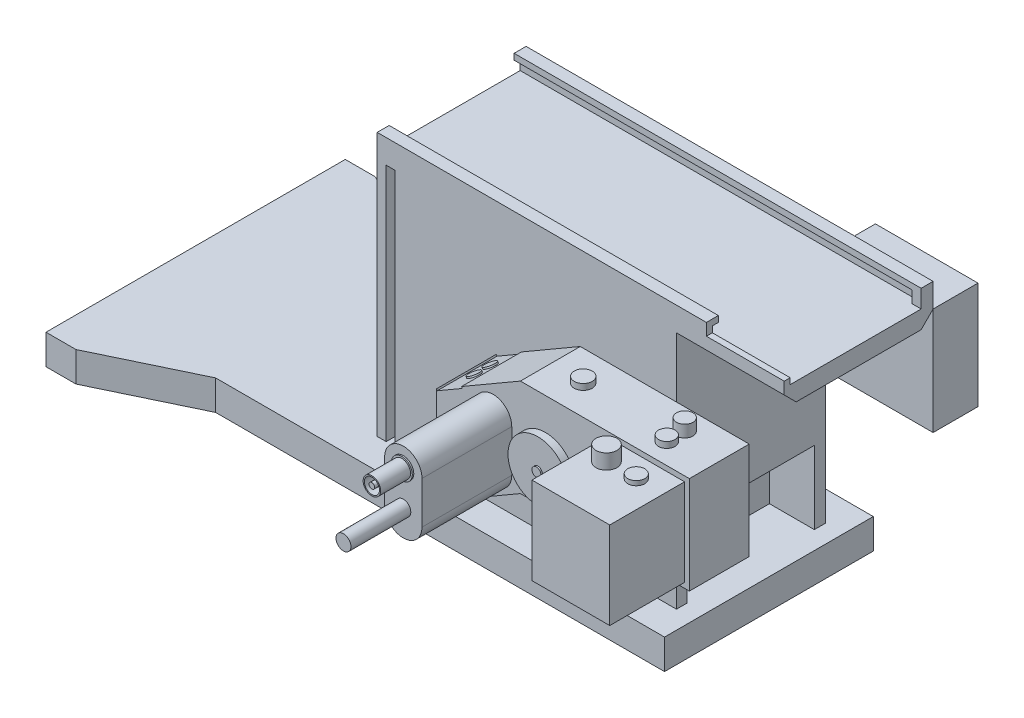
SolidWorks part; units mm, degrees
ref_plane "Front Plane" through (0, 0, 0) normal (0, 0, 1) x (1, 0, 0)
ref_plane "Top Plane" through (0, 0, 0) normal (0, 1, 0) x (1, 0, 0)
ref_plane "Right Plane" through (0, 0, 0) normal (1, 0, 0) x (0, 0, -1)
sketch "Sketch1" plane through (0, 0, 0) normal (0, 1, 0) x (1, 0, 0)
  line L0 (0, 0) -> (0, 100)
  line L1 (0, 100) -> (10, 100)
  line L2 (10, 100) -> (41.5665, 84.882)
  line L3 (41.5665, 84.882) -> (191.5665, 84.882)
  line L5 (191.5665, 15.118) -> (191.5665, 84.882)
  line L6 (41.5665, 15.118) -> (191.5665, 15.118)
  line L7 (10, 0) -> (41.5665, 15.118)
  line L8 (0, 0) -> (10, 0)
extrude "Boss-Extrude1" add sketch "Sketch1" along normal blind 10
sketch "Sketch3" plane through (0, 10, 0) normal (0, 1, 0) x (1, 0, 0)
  line L0 (85.5015, 74.9359) -> (88.5015, 74.9359)
  line L1 (85.5015, 25.1719) -> (88.5015, 25.1719)
  line L2 (85.5015, 74.9359) -> (88.5015, 74.9359)
  line L3 (88.5015, 74.9359) -> (88.5015, 71.9384)
  line L4 (185.5015, 74.9359) -> (185.5015, 25.1719)
  line L5 (91.5015, 28.1694) -> (91.5015, 25.1719)
  line L6 (88.5015, 71.9384) -> (91.5015, 71.9384)
  line L7 (85.5015, 25.1719) -> (85.5015, 74.9359)
  line L8 (91.5015, 71.9384) -> (91.5015, 74.9359)
  line L9 (88.5015, 25.1719) -> (88.5015, 28.1694)
  line L10 (88.5015, 28.1694) -> (91.5015, 28.1694)
  line L11 (91.5015, 74.9359) -> (185.5015, 74.9359)
  line L12 (91.5015, 25.1719) -> (185.5015, 25.1719)
extrude "Boss-Extrude3" add sketch "Sketch3" along normal blind 80 contours L5 L12 L4 L11 L8 L6 L3 L0 L7 L1 L9 L10
sketch "Sketch4" plane through (185.5015, 0, 0) normal (1, 0, 0) x (0, 0, -1)
  line L0 (74.9359, 10) -> (25.1719, 10) construction
  line L1 (28.7568, 10) -> (71.2432, 10)
  line L2 (28.7568, 10) -> (28.7568, 34.3784)
  line L3 (28.7568, 34.3784) -> (71.2432, 34.3784)
  line L4 (71.2432, 10) -> (71.2432, 34.3784)
extrude "Cut-Extrude2" cut sketch "Sketch4" against normal blind 15
sketch "Sketch5" plane through (0, 90, 0) normal (0, 1, 0) x (1, 0, 0)
  line L0 (96.5015, 28.1719) -> (166.5015, 28.1719)
  line L1 (96.5015, 71.9359) -> (166.5015, 71.9359)
  line L2 (166.5015, 71.9359) -> (166.5015, 28.1719)
  line L5 (96.5015, 71.9359) -> (96.5015, 28.1719)
extrude "Cut-Extrude3" cut sketch "Sketch5" against normal blind 80
sketch "Sketch6" plane through (0, 0, -74.9359) normal (0, 0, -1) x (-1, 0, 0)
  circle A0 centre (-130.8734, 50) radius 30
  circle A1 centre (-130.8734, 50) radius 30
sketch "Sketch7" plane through (185.5015, 0, 0) normal (1, 0, 0) x (0, 0, -1)
  line L0 (25.1719, 90) -> (74.9359, 90)
  line L1 (74.9359, 90) -> (74.9359, 98)
  line L2 (29.1719, 98) -> (25.1719, 98)
  line L3 (25.1719, 98) -> (25.1719, 90)
  line L4 (74.9359, 98) -> (25.1719, 98) construction
  line L5 (27.1719, 96) -> (27.1719, 92)
  line L6 (27.1719, 92) -> (29.1719, 92)
  line L8 (27.1719, 96) -> (29.1719, 96)
  line L9 (70.9359, 92) -> (70.9359, 90)
  line L10 (72.9359, 96) -> (27.1719, 96) construction
  line L11 (29.1719, 96) -> (29.1719, 98)
  line L12 (27.1719, 92) -> (72.9359, 92) construction
  line L13 (72.9359, 92) -> (72.9359, 96) construction
  line L14 (29.1719, 92) -> (29.1719, 90)
  line L15 (72.9359, 92) -> (70.9359, 92)
  line L16 (72.9359, 96) -> (72.9359, 92)
  line L17 (72.9359, 96) -> (70.9359, 96)
  line L18 (70.9359, 96) -> (70.9359, 98)
  line L19 (70.9359, 98) -> (74.9359, 98)
  line L20 (74.9359, 98) -> (74.9359, 90)
  line L21 (70.9359, 90) -> (29.1719, 90)
  dimension "D1" = 2
extrude "Boss-Extrude4" add sketch "Sketch7" along normal blind 10 and the other way blind 100
extrude "Cut-Extrude5" cut sketch "Sketch6" against normal blind 46 contours A0
sketch "Sketch8" plane through (195.5015, 0, 0) normal (1, 0, 0) x (0, 0, -1)
  line L0 (29.1719, 92) -> (29.1719, 90)
  line L1 (29.1719, 90) -> (70.9359, 90)
  line L2 (70.9359, 90) -> (70.9359, 92)
  line L3 (70.9359, 92) -> (29.1719, 92)
extrude "Boss-Extrude5" add sketch "Sketch8" along normal blind 26 and the other way blind 110
sketch "Sketch9" plane through (195.5015, 0, 0) normal (1, 0, 0) x (0, 0, -1)
  line L0 (29.1719, 90) -> (29.1719, 86)
  line L1 (29.1719, 86) -> (70.9359, 86)
  line L2 (70.9359, 86) -> (70.9359, 90)
  line L3 (70.9359, 90) -> (29.1719, 90)
extrude "Boss-Extrude6" add sketch "Sketch9" along normal blind 26 and the other way blind 10
sketch "Sketch10" plane through (195.5015, 0, 0) normal (1, 0, 0) x (0, 0, -1)
  line L0 (25.1719, 90) -> (29.1719, 86)
  line L1 (25.1719, 90) -> (29.1719, 90)
  line L2 (29.1719, 90) -> (29.1719, 86)
  line L3 (74.9359, 90) -> (70.9359, 90)
  line L4 (70.9359, 90) -> (70.9359, 86)
  line L5 (70.9359, 86) -> (74.9359, 90)
extrude "Boss-Extrude7" add sketch "Sketch10" along normal blind 26 and the other way blind 10
sketch "Sketch11" plane through (195.5015, 0, 0) normal (1, 0, 0) x (0, 0, -1)
  line L0 (70.9359, 98) -> (74.9359, 98)
  line L1 (74.9359, 98) -> (74.9359, 90)
  line L2 (74.9359, 90) -> (70.9359, 90)
  line L3 (70.9359, 90) -> (70.9359, 92)
  line L4 (70.9359, 92) -> (72.9359, 92)
  line L5 (72.9359, 92) -> (72.9359, 96)
  line L6 (72.9359, 96) -> (70.9359, 96)
  line L7 (70.9359, 96) -> (70.9359, 98)
extrude "Boss-Extrude8" add sketch "Sketch11" along normal blind 26
sketch "Sketch12" plane through (195.5015, 0, 0) normal (1, 0, 0) x (0, 0, -1)
  line L0 (25.1719, 90) -> (29.1719, 90)
  line L1 (29.1719, 90) -> (29.1719, 92)
  line L2 (29.1719, 92) -> (27.1719, 92)
  line L3 (27.1719, 92) -> (27.1719, 94)
  line L4 (27.1719, 96) -> (27.1719, 92) construction
  line L5 (27.1719, 94) -> (25.1719, 94)
  line L6 (25.1719, 98) -> (25.1719, 90) construction
  line L7 (25.1719, 94) -> (25.1719, 90)
extrude "Boss-Extrude9" add sketch "Sketch12" along normal blind 26
sketch "Sketch13" plane through (221.5015, 0, 0) normal (1, 0, 0) x (0, 0, -1)
  line L0 (70.9359, 96) -> (72.9359, 96)
  line L1 (72.9359, 96) -> (72.9359, 92)
  line L2 (72.9359, 92) -> (70.9359, 92)
  line L3 (72.9359, 92) -> (27.1719, 92) construction
  line L4 (70.9359, 92) -> (70.9359, 96)
extrude "Boss-Extrude10" add sketch "Sketch13" against normal blind 3
sketch "Sketch14" plane through (0, 0, -74.9359) normal (0, 0, -1) x (-1, 0, 0)
  line L1 (-221.5015, 90) -> (-187.2232, 90)
  line L2 (-221.5015, 90) -> (-221.5015, 54.2363)
  line L3 (-221.5015, 54.2363) -> (-187.2232, 54.2363)
  line L4 (-187.2232, 90) -> (-187.2232, 54.2363)
extrude "Boss-Extrude11" add sketch "Sketch14" along normal blind 15 separate body
sketch "Sketch15" plane through (0, 0, -25.1719) normal (0, 0, 1) x (1, 0, 0)
  line L0 (153.3564, 69.9564) -> (125.299, 53.6762)
  line L1 (153.3564, 69.9564) -> (209.8175, 69.9564)
  line L3 (153.3564, 37.396) -> (209.8175, 37.396)
  line L4 (209.8175, 69.9564) -> (209.8175, 37.396)
  line L5 (125.299, 53.6762) -> (125.299, 21.1162)
  line L6 (125.299, 21.1162) -> (153.3564, 37.396)
extrude "Boss-Extrude12" add sketch "Sketch15" along normal blind 20
sketch "Sketch16" plane through (0, 0, -5.1719) normal (0, 0, 1) x (1, 0, 0)
  line L1 (208.21, 68.2367) -> (182.1997, 68.2367)
  line L2 (208.21, 68.2367) -> (208.21, 39.1243)
  line L3 (208.21, 39.1243) -> (182.1997, 39.1243)
  line L4 (182.1997, 68.2367) -> (182.1997, 39.1243)
extrude "Boss-Extrude13" add sketch "Sketch16" along normal blind 25
sketch "Sketch17" plane through (0, 68.2367, 0) normal (0, 1, 0) x (1, 0, 0)
  circle A0 centre (189.3377, -2.0508) radius 3.5
  dimension "D1" = 7
extrude "Boss-Extrude14" add sketch "Sketch17" along normal blind 5
sketch "Sketch18" plane through (0, 68.2367, 0) normal (0, 1, 0) x (1, 0, 0)
  circle A0 centre (199.2934, -2.0508) radius 2.8464
extrude "Boss-Extrude15" add sketch "Sketch18" along normal blind 1.5
sketch "Sketch19" plane through (0, 69.9564, 0) normal (0, 1, 0) x (1, 0, 0)
  circle A0 centre (164.448, 15.0724) radius 3
extrude "Boss-Extrude16" add sketch "Sketch19" along normal blind 2
sketch "Sketch20" plane through (0, 69.9564, 0) normal (0, 1, 0) x (1, 0, 0)
  circle A0 centre (195.3657, 18.0724) radius 2.75
  circle A1 centre (195.3657, 12.0724) radius 2.75
extrude "Boss-Extrude17" add sketch "Sketch20" along normal blind 2
sketch "Sketch21" plane through (0, 71.9564, 0) normal (0, 1, 0) x (1, 0, 0)
  circle A0 centre (195.3657, 18.0724) radius 2.75
extrude "Boss-Extrude18" add sketch "Sketch21" along normal blind 2
sketch "Sketch22" plane through (0, 0, -5.1719) normal (0, 0, 1) x (1, 0, 0)
  circle A0 centre (166.6956, 54.2769) radius 1
extrude "Boss-Extrude19" add sketch "Sketch22" along normal blind 5
sketch "Sketch23" plane through (0, 0, -0.1719) normal (0, 0, 1) x (1, 0, 0)
  circle A0 centre (166.6956, 54.2769) radius 10
extrude "Boss-Extrude20" add sketch "Sketch23" along normal blind 3
sketch "Sketch24" plane through (0, 0, 2.8281) normal (0, 0, 1) x (1, 0, 0)
  circle A0 centre (166.6956, 54.2769) radius 1.5
  circle A1 centre (166.6956, 54.2769) radius 10
extrude "Cut-Extrude6" cut sketch "Sketch24" against normal blind 0.5
sketch "Sketch25" plane through (8.26, -14.2353, 0) normal (-0.5019, 0.8649, 0) x (0.8649, 0.5019, 0)
  line L0 (167.7534, 25.1719) -> (135.3149, 25.1719) construction
  line L1 (135.3149, 5.1719) -> (145.0132, 5.1719)
  line L2 (135.3149, 5.1719) -> (135.3149, 25.1719)
  line L3 (135.3149, 25.1719) -> (145.0132, 25.1719)
  line L4 (145.0132, 5.1719) -> (145.0132, 25.1719)
extrude "Cut-Extrude7" cut sketch "Sketch25" against normal blind 0.5
sketch "Sketch26" plane through (0, 0, -5.1719) normal (0, 0, 1) x (1, 0, 0)
  line L0 (144.2279, 55.3243) -> (144.2279, 41.2142) construction
  line L1 (150.4641, 55.3243) -> (150.4641, 41.2142)
  line L2 (137.9916, 55.3243) -> (137.9916, 41.2142)
  arc A0 (150.4641, 55.3243) -> (137.9916, 55.3243) centre (144.2279, 55.3243) ccw
  arc A1 (137.9916, 41.2142) -> (150.4641, 41.2142) centre (144.2279, 41.2142) ccw
  point P2 (144.2279, 48.2692)
extrude "Boss-Extrude21" add sketch "Sketch26" along normal blind 30
sketch "Sketch27" plane through (8.5109, -14.6678, 0) normal (-0.5019, 0.8649, 0) x (0.8649, 0.5019, 0)
  circle A0 centre (140.0542, 18.8765) radius 2
  circle A1 centre (140.0542, 13.5538) radius 2
extrude "Boss-Extrude22" add sketch "Sketch27" along normal blind 0.5
sketch "Sketch29" plane through (0, 0, 24.8281) normal (0, 0, 1) x (1, 0, 0)
  circle A0 centre (144.2279, 55.3243) radius 3.5
extrude "Boss-Extrude23" add sketch "Sketch29" along normal blind 0.5
sketch "Sketch30" plane through (0, 0, 25.3281) normal (0, 0, 1) x (1, 0, 0)
  circle A0 centre (144.2279, 55.3243) radius 2.9248
  circle A1 centre (144.2279, 55.3243) radius 2.5201
  circle A2 centre (144.2279, 55.3243) radius 0.9382
extrude "Boss-Extrude24" add sketch "Sketch30" along normal blind 10 contours A2 | A0 A1
sketch "Sketch31" plane through (0, 0, 24.8281) normal (0, 0, 1) x (1, 0, 0)
  circle A0 centre (144.2279, 43.7158) radius 2.5
extrude "Boss-Extrude25" add sketch "Sketch31" along normal blind 20
sketch "Sketch32" plane through (0, 0, -74.9359) normal (0, 0, -1) x (-1, 0, 0)
  circle A0 centre (-130.8734, 50) radius 33.102
extrude "Boss-Extrude26" add sketch "Sketch32" along normal blind 1 draft 20 separate body
